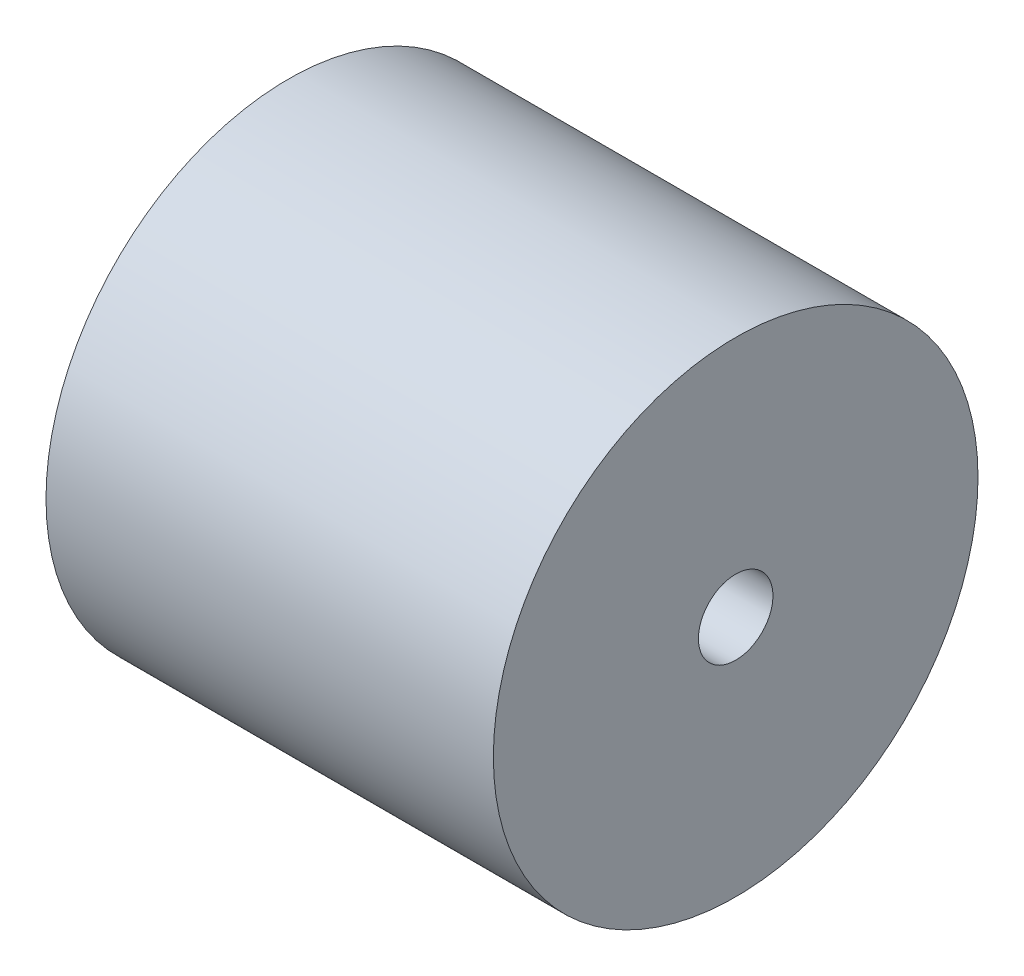
SolidWorks part; units mm, degrees
ref_plane "Front Plane" through (0, 0, 0) normal (0, 0, 1) x (1, 0, 0)
ref_plane "Top Plane" through (0, 0, 0) normal (0, 1, 0) x (1, 0, 0)
ref_plane "Right Plane" through (0, 0, 0) normal (1, 0, 0) x (0, 0, -1)
sketch "Sketch1" plane through (0, 0, 0) normal (0, 0, 1) x (1, 0, 0)
  line L2 (-50.8, 69.85) -> (-50.8, 82.55)
  line L5 (101.6, 82.55) -> (-50.8, 82.55)
  line L8 (0, 12.7) -> (101.6, 12.7)
  line L9 (101.6, 12.7) -> (101.6, 82.55)
  line L18 (-50.8, 69.85) -> (-44.45, 69.85)
  line L19 (-31.75, 57.15) -> (-31.75, 44.45)
  line L21 (0, 25.4) -> (0, 12.7)
  line L22 (0, 0) -> (101.6, 0) construction
  line L23 (-24.13, 34.925) -> (-7.62, 34.925)
  arc A7 (-44.45, 69.85) -> (-31.75, 57.15) centre (-44.45, 57.15) cw
  arc A11 (-31.75, 44.45) -> (-24.13, 34.925) centre (-22.2269, 44.258) ccw
  arc A13 (-7.62, 34.925) -> (0, 25.4) centre (-9.2735, 25.7917) cw
  point P11 (0, 0)
  point P14 (0, 0)
  point P21 (0, 0)
  point P22 (0, 0)
  dimension "D1" = 12.7
  dimension "D4" = 12.7
  dimension "D5" = 12.7
  dimension "D8" = 31.75
  dimension "D9" = 6.35
  dimension "D10" = 7.62
  dimension "D13" = 19.05
  dimension "D11" = 9.525
  dimension "D2" = 101.6
  dimension "D3" = 69.85
  dimension "D6" = 152.4
  dimension "D7" = 12.7
  dimension "D12" = 12.7
  dimension "D14" = 16.51
  dimension "D15" = 9.525
  dimension "D16" = 0
  dimension "D17" = 9.2735
revolve "Revolve2" add sketch "Sketch1" angle 360 about L22
